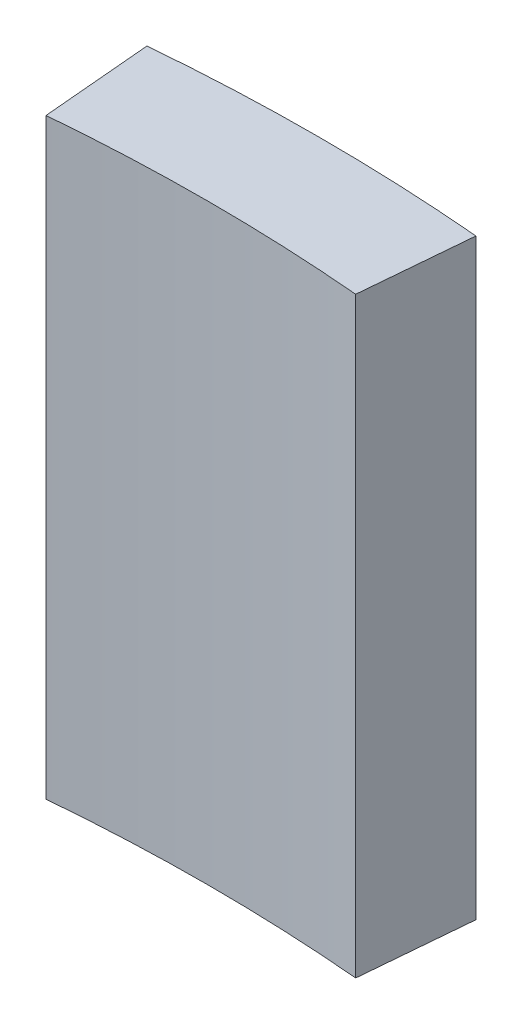
SolidWorks part; units mm, degrees
material "PVC Rigid"
ref_plane "Front Plane" through (0, 0, 0) normal (0, 0, 1) x (1, 0, 0)
ref_plane "Top Plane" through (0, 0, 0) normal (0, 1, 0) x (1, 0, 0)
ref_plane "Right Plane" through (0, 0, 0) normal (1, 0, 0) x (0, 0, -1)
sketch "Sketch1" plane through (0, 0, 0) normal (0, 0, 1) x (1, 0, 0)
  line L0 (0, 0) -> (0, 50.8)
  dimension "D1" = 50.8
other "Pipe (standard, s40) P12(1)"
ref_plane "Plane1" through (0, 0, 0) normal (0, 1, 0) x (-1, 0, 0)
sketch "Sketch11" plane through (0, 0, 0) normal (0, 1, 0) x (-1, 0, 0)
  circle A0 centre (0, 0) radius 152.4
  circle A1 centre (0, 0) radius 161.925
  point P3 (0, 0)
  dimension "In_dia" = 304.8
  dimension "Out_dia" = 323.85
sketch "Sketch12" plane through (0, 50.8, 0) normal (0, 1, 0) x (1, 0, 0)
  line L0 (0, 0) -> (0, 161.925) construction
  line L1 (0, 0) -> (-14.1127, 161.3088)
  line L2 (0, 0) -> (14.1127, 161.3088)
  circle A0 centre (0, 0) radius 161.925 construction
  arc A1 (-14.1127, 161.3088) -> (14.1127, 161.3088) centre (0, 0) ccw
  dimension "D1" = 10
  dimension "D2" = 5
extrude "Cut-Extrude1" cut sketch "Sketch12" against normal through all
